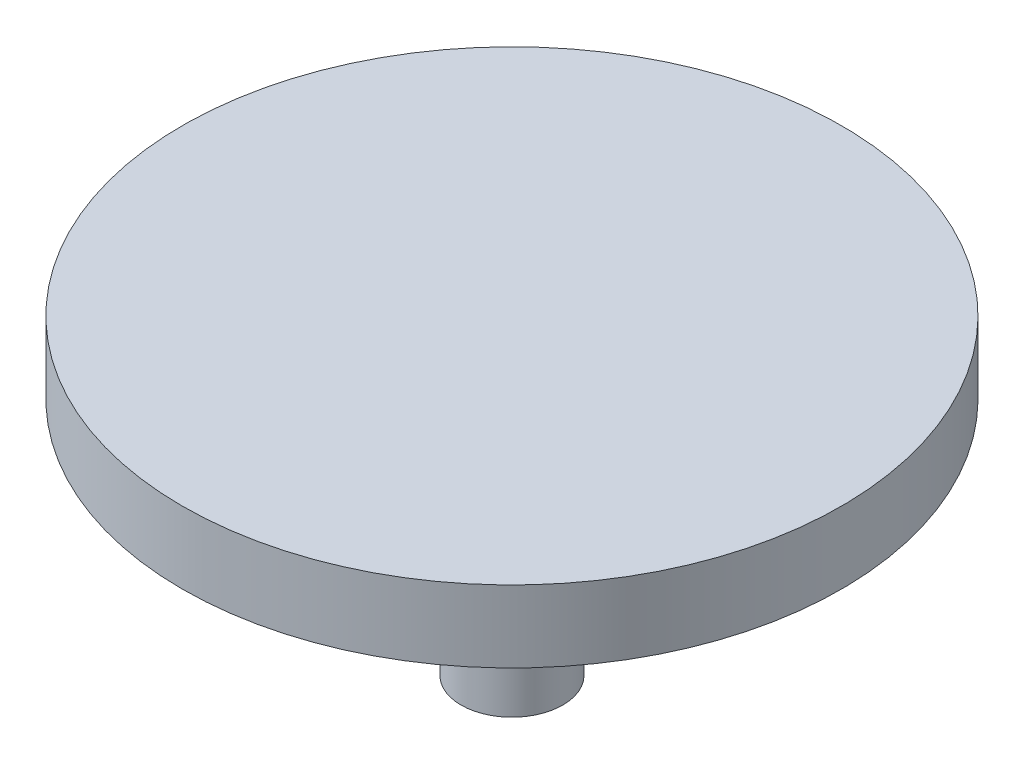
SolidWorks part; units mm, degrees
material "ABS"
ref_plane "Plano frontal" through (0, 0, 0) normal (0, 0, 1) x (1, 0, 0)
ref_plane "Plano superior" through (0, 0, 0) normal (0, 1, 0) x (1, 0, 0)
ref_plane "Plano direito" through (0, 0, 0) normal (1, 0, 0) x (0, 0, -1)
sketch "Esboço1" plane through (0, 0, 0) normal (0, 1, 0) x (1, 0, 0)
  circle A0 centre (0, 0) radius 4.25
  dimension "D1" = 8.5
extrude "Ressalto-extrusão1" add sketch "Esboço1" along normal blind 20
sketch "Esboço2" plane through (0, 20, 0) normal (0, 1, 0) x (1, 0, 0)
  circle A0 centre (0, 0) radius 27.5
  dimension "D1" = 55
extrude "Ressalto-extrusão2" add sketch "Esboço2" along normal blind 6
